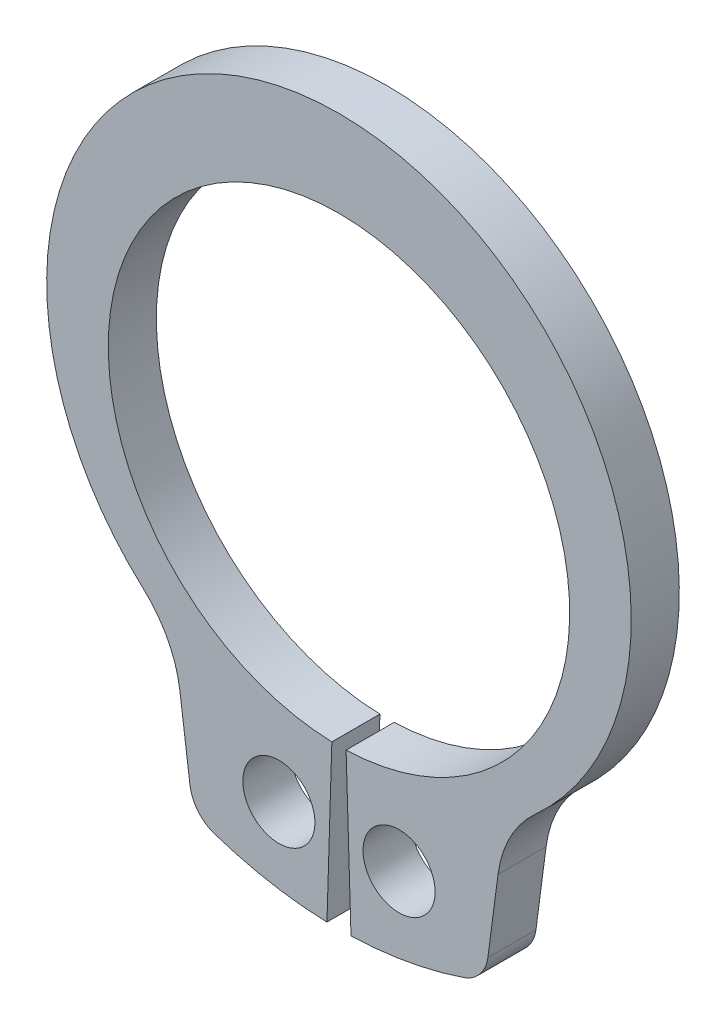
SolidWorks part; units mm, degrees
ref_plane "Plane1" through (0, 0, 0) normal (0, 0, 1) x (1, 0, 0)
ref_plane "Plane2" through (0, 0, 0) normal (0, 1, 0) x (1, 0, 0)
ref_plane "Plane3" through (0, 0, 0) normal (1, 0, 0) x (0, 0, -1)
sketch "Clipboard" plane through (0, 0, 0) normal (0, 0, 1) x (1, 0, 0)
  line L0 (0, 0) -> (1.8, 0)
  line L1 (0, 0) -> (0, 0.9)
  line L2 (0, 0) -> (0, -3.3)
  circle A0 centre (0, 0) radius 0.75
  circle A1 centre (0, 0) radius 5
  dimension "HoleDia" = 1.5
  dimension "ShaftDia" = 10
  dimension "LargeSection" = 1.8
  dimension "SmallSection" = 0.9
  dimension "LugSection" = 3.3
sketch "BodySke" plane through (0, 0, 0) normal (0, 0, 1) x (1, 0, 0)
  line L0 (-1.5431, 0) -> (1.5431, 0) construction
  line L1 (0, 0) -> (0, 6.6) construction
  line L2 (0.1481, -4.7977) -> (0.25, -8.0961)
  line L3 (-0.1481, -4.7977) -> (-0.25, -8.0961)
  line L4 (0, 0) -> (5.6861, -5.7688) construction
  line L5 (0, 0) -> (-5.6861, -5.7688) construction
  line L7 (3.3097, -5.4559) -> (3.0984, -7.0605)
  line L8 (-3.3097, -5.4559) -> (-3.0984, -7.0605)
  circle A0 centre (0, 0) radius 4.8 construction
  arc A1 (0.1481, -4.7977) -> (-0.1481, -4.7977) centre (0, 0) ccw
  arc A2 (4.0013, -4.0595) -> (-4.0013, -4.0595) centre (0, 0.5193) ccw construction
  arc A3 (0.25, -8.0961) -> (2.5951, -7.673) centre (0, 0) ccw
  arc A4 (4.0784, -3.991) -> (3.3097, -5.4559) centre (5.6861, -5.7688) ccw
  arc A5 (-3.3097, -5.4559) -> (-4.0784, -3.991) centre (-5.6861, -5.7688) ccw
  arc A6 (-2.5951, -7.673) -> (-0.25, -8.0961) centre (0, 0) ccw
  arc A7 (4.0784, -3.991) -> (-4.0784, -3.991) centre (0, 0.5193) ccw
  arc A8 (-3.2816, -5.6686) -> (3.2816, -5.6686) centre (0, 0) ccw construction
  circle A9 centre (1.25, -6.4296) radius 0.75
  circle A10 centre (-1.25, -6.4296) radius 0.75
  arc A11 (3.0984, -7.0605) -> (2.5951, -7.673) centre (2.3548, -6.9626) cw
  arc A12 (-3.0984, -7.0605) -> (-2.5951, -7.673) centre (-2.3548, -6.9626) ccw
  point P28 (3.0395, -7.5081)
  point P31 (-3.0395, -7.5081)
  dimension "HoleDia" = 1.5
  dimension "GrooveDia" = 9.6
  dimension "LugRad" = 8.1
  dimension "HoleOffsetRad" = 6.55
  dimension "D3" = 0.75
  dimension "LargeRad" = 6.6
  dimension "SmallRad" = 5.7
  dimension "SmallAngle" = 89.172
  dimension "D2" = 15
  dimension "HoleSpacing" = 2.5
  dimension "Gap" = 0.5
extrude "Body" add sketch "BodySke" against normal blind 1
sketch "NotSke" plane through (0, 0, 0) normal (0, 0, 1) x (1, 0, 0)
  line L0 (1.25, -5.6796) -> (1.25, -7.1796)
  line L1 (1.25, -7.1796) -> (-1.25, -7.1796)
  line L2 (-1.25, -7.1796) -> (-1.25, -5.6796)
  line L3 (-1.25, -5.6796) -> (1.25, -5.6796)
  circle A0 centre (1.25, -6.4296) radius 0.75 construction
  circle A1 centre (-1.25, -6.4296) radius 0.75 construction
extrude "Notch" [suppressed] cut sketch "NotSke" against normal through all
sketch "UnlSke" plane through (0, 0, 0) normal (0, 0, 1) x (1, 0, 0)
  line L0 (-2.4461, -7.7218) -> (-1.4495, -4.5759)
  line L1 (2.4461, -7.7218) -> (1.4495, -4.5759)
  arc A0 (1.4495, -4.5759) -> (-1.4495, -4.5759) centre (0, 0) ccw
  arc A1 (2.4461, -7.7218) -> (-2.4461, -7.7218) centre (0, 0) ccw
  arc A2 (0.25, -8.0961) -> (2.5951, -7.673) centre (0, 0) ccw construction
  arc A3 (0.1481, -4.7977) -> (-0.1481, -4.7977) centre (0, 0) ccw construction
  circle A4 centre (-1.25, -6.4296) radius 0.75 construction
  circle A5 centre (1.25, -6.4296) radius 0.75 construction
extrude "Unlug" [suppressed] add sketch "UnlSke" against normal through all
equation "' \"ShaftDia@Clipboard\" = 3"
equation "' \"Thickness@Body\" = 0.4"
equation "' \"GrooveDia@BodySke\" = 2.8"
equation "' \"LugSection@Clipboard\" = 1.9"
equation "' \"LargeSection@Clipboard\" = 0.8"
equation "' \"HoleDia@Clipboard\" = 1.0"
equation "' \"ShaftDia@Clipboard\" = 10"
equation "' \"Thickness@Body\" = 1.0"
equation "' \"GrooveDia@BodySke\" = 9.6"
equation "' \"LugSection@Clipboard\" = 3.3"
equation "' \"LargeSection@Clipboard\" = 1.8"
equation "' \"HoleDia@Clipboard\" = 1.5"
equation "\"SmallSection@Clipboard\" = \"LargeSection@Clipboard\" * 0.5"
equation "\"Gap@BodySke\" =  \"Thickness@Body\" / 2"
equation "\"LargeRad@BodySke\" =  \"GrooveDia@BodySke\" / 2 +  \"LargeSection@Clipboard\""
equation "\"SmallRad@BodySke\" =  \"GrooveDia@BodySke\" / 2 +  \"SmallSection@Clipboard\""
equation "\"LugRad@BodySke\" = \"GrooveDia@BodySke\" / 2 + \"LugSection@Clipboard\""
equation "\"HoleOffsetRad@BodySke\" = (  \"ShaftDia@Clipboard\" / 2 + \"LugRad@BodySke\" ) / 2"
equation "\"HoleSpacing@BodySke\" = \"Gap@BodySke\"  * 2 +  \"HoleDia@Clipboard\""
equation "\"HoleDia@BodySke\" =  \"HoleDia@Clipboard\""
equation "\"SmallAngle@BodySke\" = atn(\"HoleSpacing@BodySke\" / 2 / sqr(\"HoleOffsetRad@BodySke\"  * \"HoleOffsetRad@BodySke\" - (\"HoleSpacing@BodySke\" / 2) * (\"HoleSpacing@BodySke\" / 2) ))  * 7 *  (\"LargeRad@BodySke\" / \"SmallRad@BodySke\")* ( 180 / 3.141593)"
